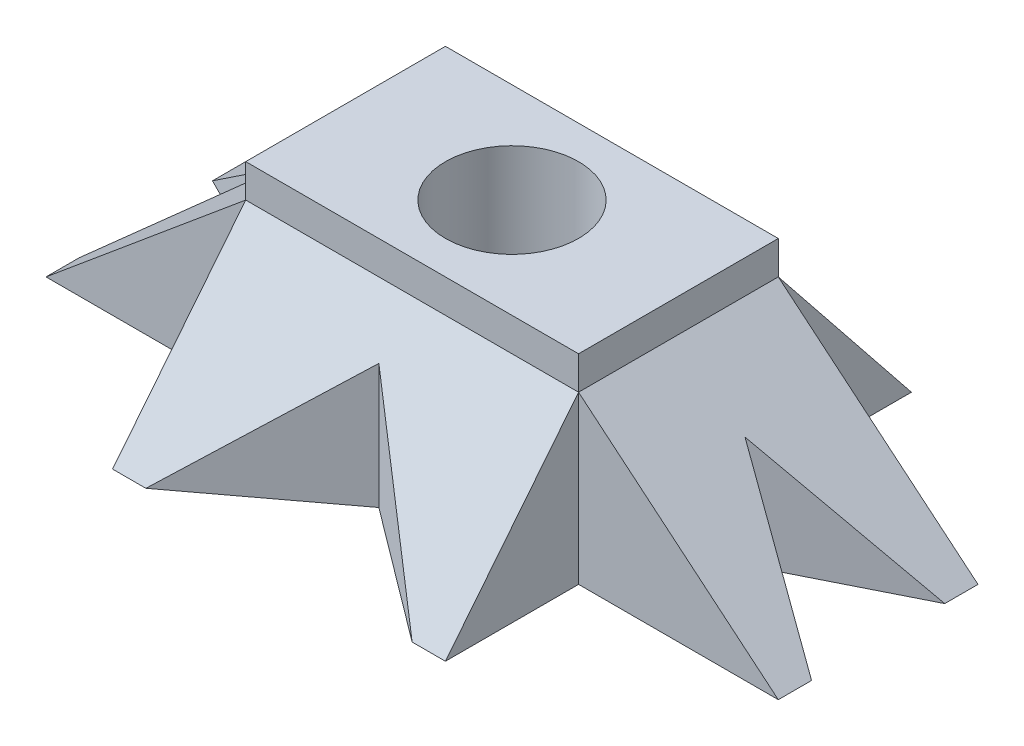
SolidWorks part; units mm, degrees
ref_plane "Front Plane" through (0, 0, 0) normal (0, 0, 1) x (1, 0, 0)
ref_plane "Top Plane" through (0, 0, 0) normal (0, 1, 0) x (1, 0, 0)
ref_plane "Right Plane" through (0, 0, 0) normal (1, 0, 0) x (0, 0, -1)
sketch "Sketch1" plane through (0, 0, 0) normal (0, 1, 0) x (1, 0, 0)
  line L1 (-50, 30) -> (50, 30)
  line L2 (-50, 30) -> (-50, -30)
  line L3 (-50, -30) -> (50, -30)
  line L4 (50, 30) -> (50, -30)
  line L5 (-50, 30) -> (50, -30) construction
  line L6 (-50, -30) -> (50, 30) construction
  circle A0 centre (0, 0) radius 20
  point P0 (0, 0)
  dimension "D3" = 40
  dimension "D1" = 60
  dimension "D2" = 100
extrude "Boss-Extrude1" add sketch "Sketch1" along normal blind 60
sketch "Sketch3" plane through (0, 0, 0) normal (0, 0, 1) x (1, 0, 0)
  line L0 (50, 0) -> (50, 50)
  line L1 (50, 60) -> (50, 0) construction
  line L2 (50, 50) -> (110, 0)
  line L3 (110, 0) -> (50, 0)
  line L4 (0, 0) -> (0, 60) construction
  line L5 (-50, 0) -> (50, 0) construction
  line L6 (-50, 60) -> (50, 60) construction
  line L7 (-110, 0) -> (-50, 0)
  line L8 (-50, 50) -> (-110, 0)
  line L9 (-50, 0) -> (-50, 50)
  dimension "D1" = 50
  dimension "D2" = 60
extrude "Boss-Extrude2" add sketch "Sketch3" along normal mid plane 60
sketch "Sketch4" plane through (0, 0, 0) normal (1, 0, 0) x (0, 0, -1)
  line L0 (-30, 0) -> (-30, 50)
  line L1 (-30, 0) -> (-30, 50) construction
  line L2 (-30, 50) -> (-70, 0)
  line L3 (-70, 0) -> (-30, 0)
  line L4 (0, 0) -> (0, 50) construction
  line L5 (-30, 0) -> (30, 0) construction
  line L6 (-30, 50) -> (30, 50) construction
  line L7 (30, 0) -> (30, 50)
  line L8 (70, 0) -> (30, 0)
  line L9 (30, 50) -> (70, 0)
  dimension "D1" = 50
  dimension "D2" = 40
extrude "Boss-Extrude3" add sketch "Sketch4" along normal mid plane 100
sketch "Sketch5" plane through (0, 0, 0) normal (0, 1, 0) x (1, 0, 0)
  line L0 (-40, -70) -> (0, -40)
  line L1 (50, -70) -> (-50, -70) construction
  line L2 (0, -40) -> (40, -70)
  line L3 (0, 0) -> (0, -50000) construction
  line L4 (-50, -30) -> (50, -30) construction
  line L5 (0, 0) -> (50000, 0) construction
  line L6 (50, -30) -> (50, 30) construction
  line L7 (-40, -70) -> (40, -70)
  line L8 (0, 40) -> (40, 70)
  line L9 (-40, 70) -> (0, 40)
  line L10 (-40, 70) -> (40, 70)
  line L11 (110, -20) -> (70, 0)
  line L12 (110, -30) -> (110, 30) construction
  line L13 (70, 0) -> (110, 20)
  line L14 (110, 20) -> (110, -20)
  line L15 (-110, 20) -> (-110, -20)
  line L16 (-70, 0) -> (-110, 20)
  line L17 (-110, -20) -> (-70, 0)
  point P12 (0, -30)
  point P18 (50, 0)
  dimension "D3" = 30
  dimension "D4" = 10
  dimension "D5" = 10
  dimension "D6" = 40
extrude "Cut-Extrude1" cut sketch "Sketch5" along normal through all
equation "\"Length\" = 100"
equation "\"Width\"= 60"
equation "\"D1@Sketch1\"=\"Width\""
equation "\"D2@Sketch1\"=\"Length\""
equation "\"Height\" = 50"
equation "\"D1@Boss-Extrude1\"=\"Height\""
equation "\"D1@Sketch3\"=\"Height\""
equation "\"D1@Boss-Extrude2\"=\"Width\""
equation "\"D1@Sketch4\"=\"Height\""
equation "\"D1@Boss-Extrude3\"=\"Length\""
equation "\"D1@Sketch5\"=\"Length\"*1/10"
equation "\"D2@Sketch5\"=\"Length\"*1/10"
equation "\"D4@Sketch5\"=\"Width\"*1/6"
equation "\"D5@Sketch5\"=\"Width\"*1/6"
